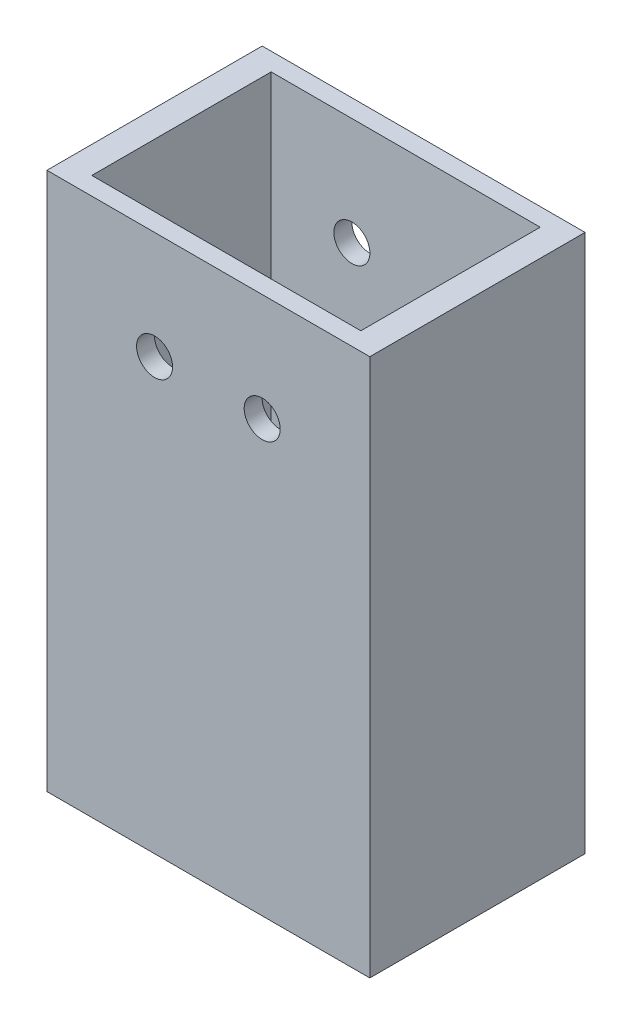
SolidWorks part; units mm, degrees
ref_plane "Front Plane" through (0, 0, 0) normal (0, 0, 1) x (1, 0, 0)
ref_plane "Top Plane" through (0, 0, 0) normal (0, 1, 0) x (1, 0, 0)
ref_plane "Right Plane" through (0, 0, 0) normal (1, 0, 0) x (0, 0, -1)
sketch "Sketch1" plane through (0, 0, 0) normal (0, 1, 0) x (1, 0, 0)
  line L1 (-38.1, -25.4) -> (38.1, -25.4)
  line L2 (-38.1, -25.4) -> (-38.1, 25.4)
  line L3 (-38.1, 25.4) -> (38.1, 25.4)
  line L4 (38.1, -25.4) -> (38.1, 25.4)
  line L5 (-38.1, -25.4) -> (38.1, 25.4) construction
  line L6 (-38.1, 25.4) -> (38.1, -25.4) construction
  line L7 (-31.75, -21.1667) -> (31.75, -21.1667)
  line L8 (-31.75, -21.1667) -> (-31.75, 21.1667)
  line L9 (-31.75, 21.1667) -> (31.75, 21.1667)
  line L10 (31.75, -21.1667) -> (31.75, 21.1667)
  line L11 (-31.75, -21.1667) -> (31.75, 21.1667) construction
  line L12 (-31.75, 21.1667) -> (31.75, -21.1667) construction
  point P0 (0, 0)
  point P6 (0, 0)
  dimension "D1" = 76.2
  dimension "D2" = 50.8
  dimension "D3" = 6.35
extrude "Boss-Extrude1" add sketch "Sketch1" along normal mid plane 127
sketch "Sketch2" plane through (0, 0, 25.4) normal (0, 0, 1) x (1, 0, 0)
  point P0 (-12.7, 38.1)
  point P1 (12.7, 38.1)
  point P3 (-74.8493, 59.8642)
hole_wizard "Tap Drill for M10x1.5 Tap1" positions "Sketch4" profile "Sketch5" hole size "M10x1.5" standard "ANSI Metric" end condition through all
sketch "Sketch4" plane through (0, 0, 25.4) normal (0, 0, 1) x (1, 0, 0)
  line L1 (-38.1, 63.5) -> (38.1, 63.5) construction
  point P0 (-12.7, 38.1)
  point P3 (12.7, 38.1)
  dimension "D1" = 25.4
  dimension "D2" = 25.4
sketch "Sketch5" plane through (-12.7, 38.1, 25.4) normal (1, 0, 0) x (0, -1, 0)
  line L0 (0, 0) -> (0, 50.8)
  line L1 (0, 50.8) -> (4.25, 50.8)
  line L2 (4.25, 50.8) -> (4.25, 0)
  line L5 (4.25, 0) -> (0, 0)
  line L11 (0, -6.35) -> (0, 107.95) construction
  dimension "Thru Hole Dia." = 8.5
  dimension "Thru Hole Depth" = 50.8
